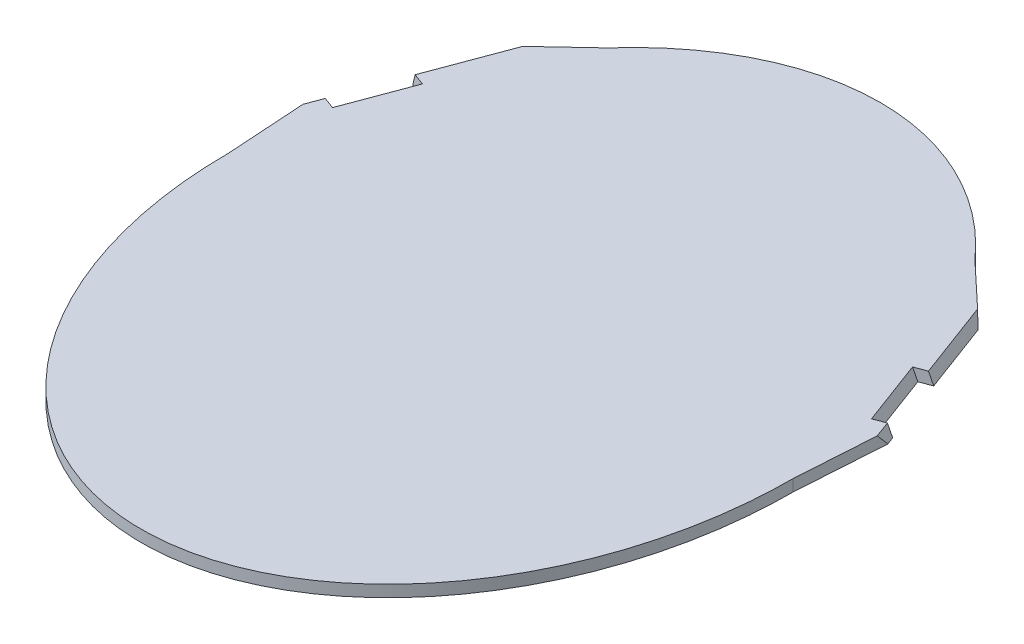
SolidWorks part; units mm, degrees
ref_plane "Front Plane" through (0, 0, 0) normal (0, 0, 1) x (1, 0, 0)
ref_plane "Top Plane" through (0, 0, 0) normal (0, 1, 0) x (1, 0, 0)
ref_plane "Right Plane" through (0, 0, 0) normal (1, 0, 0) x (0, 0, -1)
sketch "Sketch1" plane through (0, 0, 0) normal (0, 1, 0) x (1, 0, 0)
  ellipse E1 centre (0, 0) end of major axis (0, 380) minor radius 290
  dimension "D3" = 580
  dimension "D4" = 760
extrude "Boss-Extrude1" add sketch "Sketch1" along normal blind 12
sketch "Sketch2" plane through (0, 12, 0) normal (0, 1, 0) x (1, 0, 0)
  line L14 (-267.8433, 167.0099) -> (-255.9333, 162.5662)
  line L15 (-255.9333, 162.5662) -> (-281.0412, 95.2708)
  line L16 (-281.0412, 95.2708) -> (-292.9513, 99.7145)
  line L17 (-292.9513, 99.7145) -> (-295.9084, 91.7888)
  line L18 (-295.9084, 91.7888) -> (-290, 0)
  line L19 (290, 0) -> (295.9084, 91.7888)
  line L20 (295.9084, 91.7888) -> (292.9513, 99.7145)
  line L21 (292.9513, 99.7145) -> (281.0412, 95.2708)
  line L22 (281.0412, 95.2708) -> (255.9333, 162.5662)
  line L23 (255.9333, 162.5662) -> (267.8433, 167.0099)
  line L24 (267.8433, 167.0099) -> (240.7419, 239.6482)
  line L25 (240.7419, 239.6482) -> (188.9895, 288.2251)
  line L26 (-188.9895, 288.2251) -> (-240.7419, 239.6482)
  line L27 (-240.7419, 239.6482) -> (-267.8433, 167.0099)
  line L28 (-267.8433, 167.0099) -> (-255.9333, 162.5662)
  line L29 (-255.9333, 162.5662) -> (-281.0412, 95.2708)
  line L30 (-281.0412, 95.2708) -> (-292.9513, 99.7145)
  line L31 (-292.9513, 99.7145) -> (-295.9084, 91.7888)
  line L32 (-295.9084, 91.7888) -> (-290, 0)
  line L33 (290, 0) -> (295.9084, 91.7888)
  line L34 (295.9084, 91.7888) -> (292.9513, 99.7145)
  line L35 (292.9513, 99.7145) -> (281.0412, 95.2708)
  line L36 (281.0412, 95.2708) -> (255.9333, 162.5662)
  line L37 (255.9333, 162.5662) -> (267.8433, 167.0099)
  line L38 (267.8433, 167.0099) -> (240.7419, 239.6482)
  line L39 (240.7419, 239.6482) -> (188.9895, 288.2251)
  line L40 (-188.9895, 288.2251) -> (-240.7419, 239.6482)
  line L41 (-240.7419, 239.6482) -> (-267.8433, 167.0099)
  ellipse E3 centre (0, 0) end of major axis (0, 380) minor radius 290 (-290, 0) -> (290, 0) ccw
  ellipse E4 centre (0, 0) end of major axis (0, 380) minor radius 290 (188.9895, 288.2251) -> (-188.9895, 288.2251) ccw
  ellipse E5 centre (0, 0) end of major axis (0, 380) minor radius 290 (-290, 0) -> (290, 0) ccw
  ellipse E6 centre (0, 0) end of major axis (0, 380) minor radius 290 (188.9895, 288.2251) -> (-188.9895, 288.2251) ccw
  dimension "D1" = 0
extrude "Boss-Extrude2" add sketch "Sketch2" against normal blind 12
ref_plane "Plane1" through (258.2545, 96.3551, -96.3551) normal (0.8844, 0.33, -0.33) x (-0.3092, -0.1154, -0.944)
sketch "Sketch4" plane through (258.2545, 96.3551, -96.3551) normal (0.8844, 0.33, -0.33) x (-0.3092, -0.1154, -0.944)
  line L0 (1.4928, -85.6249) -> (-0.145, -72.3215)
  line L1 (-0.145, -72.3215) -> (71.1434, -63.5447)
  line L2 (71.1434, -63.5447) -> (72.7813, -76.8481)
  line L3 (72.7813, -76.8481) -> (74.8472, -93.6282)
  line L4 (74.8472, -93.6282) -> (3.5588, -102.405)
  line L5 (3.5588, -102.405) -> (1.4928, -85.6249)
extrude "Cut-Extrude1" cut sketch "Sketch4" against normal blind 12
mirror "Mirror1" about plane through (0, 0, 0) normal (1, 0, 0) of "Cut-Extrude1"
sketch "Sketch8" plane through (258.2545, 96.3551, -96.3551) normal (0.8844, 0.33, -0.33) x (-0.3092, -0.1154, -0.944)
  line L1 (-117.3026, 23.0684) -> (238.4926, 23.0684)
  line L2 (-117.3026, 23.0684) -> (-117.3026, -239.4472)
  line L3 (-117.3026, -239.4472) -> (238.4926, -239.4472)
  line L4 (238.4926, 23.0684) -> (238.4926, -239.4472)
extrude "Cut-Extrude2" cut sketch "Sketch8" along normal through all
mirror "Mirror2" about plane through (0, 0, 0) normal (1, 0, 0) of "Cut-Extrude2"
